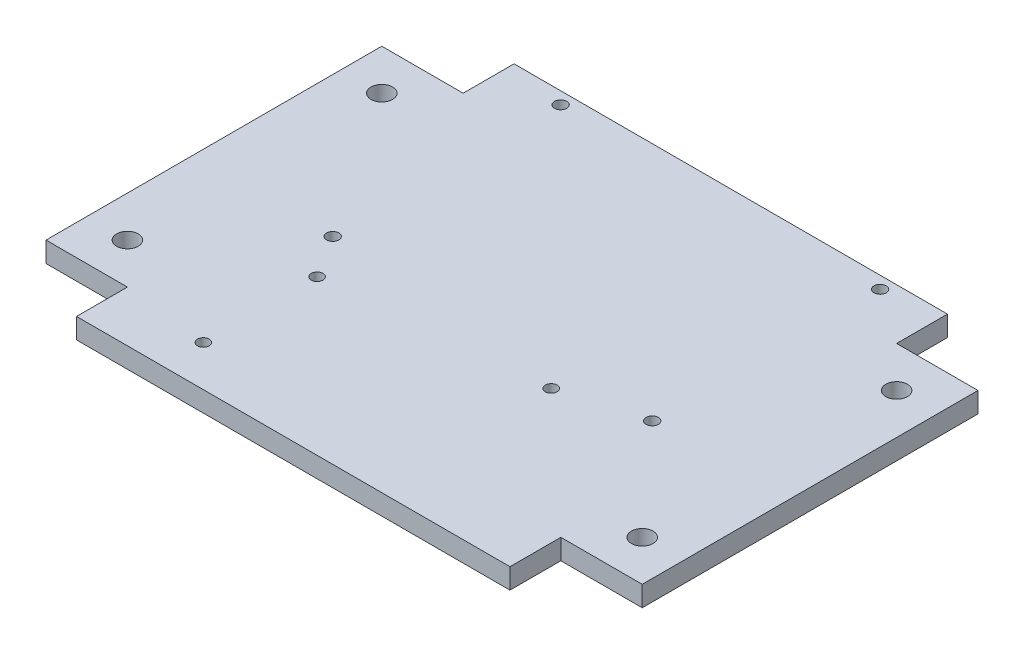
SolidWorks part; units mm, degrees
ref_plane "Alzado" through (0, 0, 0) normal (0, 0, 1) x (1, 0, 0)
ref_plane "Planta" through (0, 0, 0) normal (0, 1, 0) x (1, 0, 0)
ref_plane "Vista lateral" through (0, 0, 0) normal (1, 0, 0) x (0, 0, -1)
sketch "Croquis1" plane through (0, 0, 0) normal (0, 1, 0) x (1, 0, 0)
  line L0 (53.25, -50) -> (53.25, -37.5)
  line L1 (-73.25, 57.5) -> (73.25, 57.5) construction
  line L2 (-73.25, 57.5) -> (-73.25, -57.5) construction
  line L3 (-73.25, -57.5) -> (73.25, -57.5) construction
  line L4 (73.25, 57.5) -> (73.25, -57.5) construction
  line L7 (-73.25, -37.5) -> (-53.25, -37.5)
  line L8 (-53.25, -50) -> (-53.25, -37.5)
  line L11 (53.25, -37.5) -> (73.25, -37.5)
  line L13 (-73.25, 45) -> (-53.25, 45)
  line L14 (-53.25, 45) -> (-53.25, 57.5)
  line L16 (53.25, 45) -> (53.25, 57.5)
  line L19 (53.25, 45) -> (73.25, 45)
  line L20 (-73.25, 57.5) -> (-53.25, 57.5) [skipped]
  line L22 (73.25, -50) -> (73.25, -37.5) [skipped]
  line L23 (73.25, 45) -> (73.25, 57.5) [skipped]
  line L24 (-53.25, 57.5) -> (53.25, 57.5)
  line L25 (73.25, 45) -> (73.25, -37.5)
  line L26 (53.25, -50) -> (-53.25, -50)
  line L27 (-73.25, -37.5) -> (-73.25, 45)
  dimension "D1" = 146.5
  dimension "D2" = 115
  dimension "D3" = 57.5
  dimension "D4" = 73.25
  dimension "D5" = 20
  dimension "D6" = 12.5
  dimension "D7" = 2
  dimension "D8" = 2
  dimension "D9" = 2
extrude "Saliente-Extruir1" add sketch "Croquis1" along normal blind 5
sketch "Croquis2" plane through (0, 5, 0) normal (0, 1, 0) x (1, 0, 0)
  line L0 (-53.25, 45) -> (-73.25, 45) construction
  line L1 (-73.25, 45) -> (-73.25, -37.5) construction
  line L2 (-73.25, -37.5) -> (-53.25, -37.5) construction
  circle A0 centre (-63.25, 35) radius 2.65
  circle A1 centre (-63.25, -27.5) radius 2.65
  circle A2 centre (63.25, 35) radius 2.65
  circle A3 centre (63.25, -27.5) radius 2.65
  dimension "D1" = 5.3
  dimension "D2" = 10
  dimension "D3" = 10
  dimension "D4" = 10
  dimension "D5" = 10
  dimension "D6" = 2
extrude "Cortar-Extruir1" cut sketch "Croquis2" against normal blind 5
sketch "Croquis5" plane through (0, 5, 0) normal (0, 1, 0) x (1, 0, 0)
  line L0 (53.25, 57.5) -> (-53.25, 57.5) construction
  circle A0 centre (-38.7977, 54.5) radius 1.5
  circle A1 centre (39.7023, 54.5) radius 1.5
  circle A2 centre (-38.7977, -1.5) radius 1.5
  circle A3 centre (39.7023, -1.5) radius 1.5
  circle A4 centre (-32.1319, -39.96) radius 1.445
  circle A5 centre (-32.1319, -12) radius 1.445
  circle A6 centre (20.3881, -7) radius 1.445
  point P14 (0, 0)
  point P15 (0, 0)
  dimension "D14" = 3
  dimension "D15" = 2.89
  dimension "D1" = 78.5
  dimension "D2" = 56
  dimension "D3" = 56
  dimension "D4" = 78.5
  dimension "D5" = 27.96
  dimension "D6" = 6.6658
  dimension "D7" = 6.6658
  dimension "D8" = 52.52
  dimension "D9" = 32.96
  dimension "D10" = 19.3142
  dimension "D11" = 3
  dimension "D12" = 94.46
  dimension "D13" = 10.5
extrude "Cortar-Extruir2" cut sketch "Croquis5" against normal blind 10
